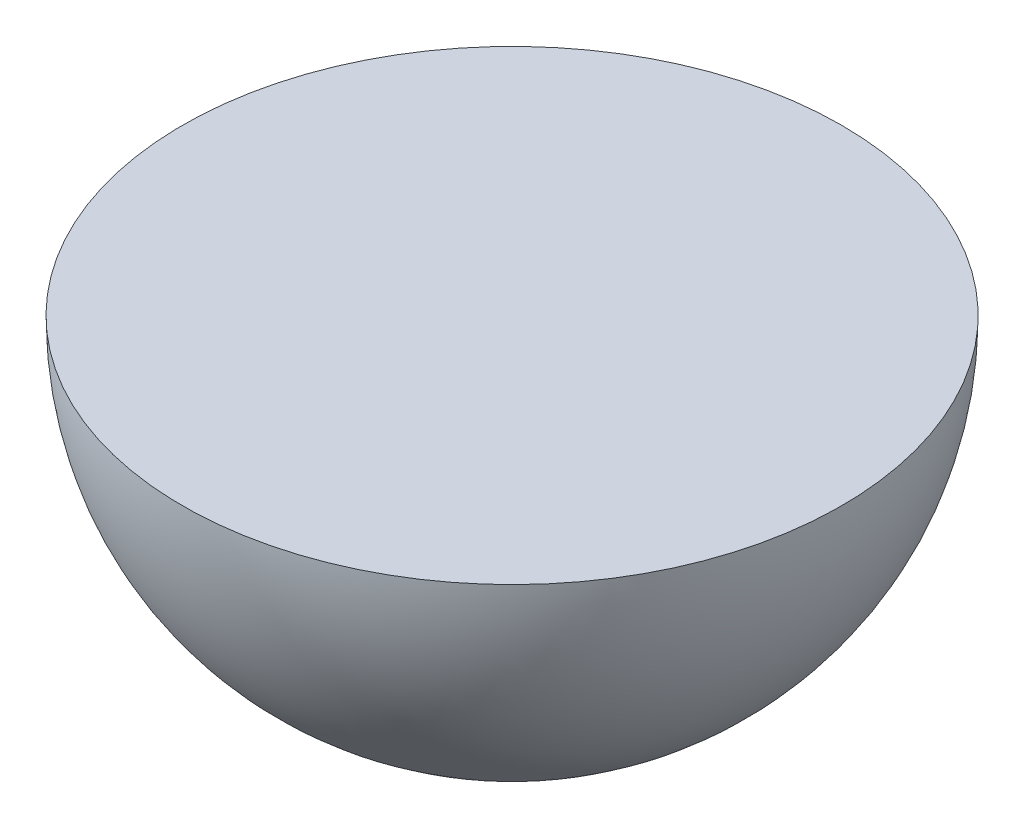
SolidWorks part; units mm, degrees
ref_plane "Front Plane" through (0, 0, 0) normal (0, 0, 1) x (1, 0, 0)
ref_plane "Top Plane" through (0, 0, 0) normal (0, 1, 0) x (1, 0, 0)
ref_plane "Right Plane" through (0, 0, 0) normal (1, 0, 0) x (0, 0, -1)
sketch "Sketch1" plane through (0, 0, 0) normal (0, 1, 0) x (1, 0, 0)
  line L0 (-2.5, 0) -> (2.5, 0)
  arc A0 (2.5, 0) -> (-2.5, 0) centre (0, 0) ccw
  dimension "D1" = 5
revolve "Revolve1" add sketch "Sketch1" angle 180 about L0
